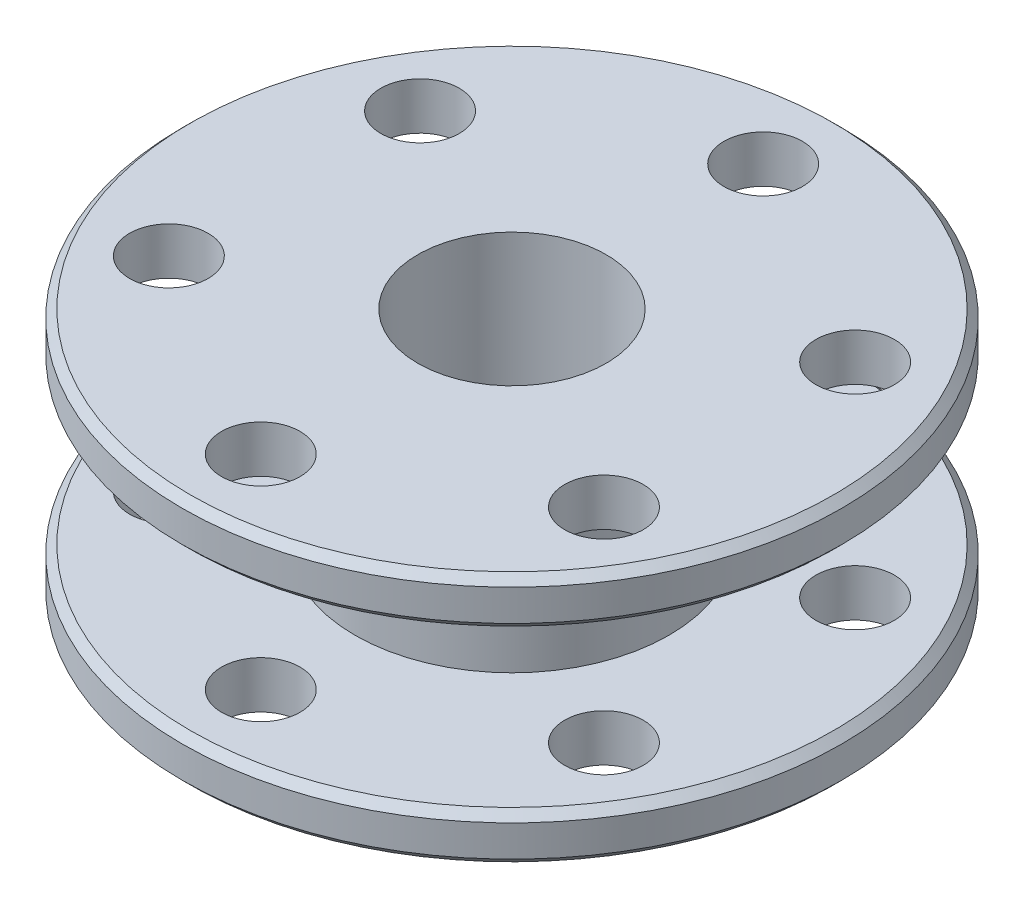
SolidWorks part; units mm, degrees
ref_plane "Front Plane" through (0, 0, 0) normal (0, 0, 1) x (1, 0, 0)
ref_plane "Top Plane" through (0, 0, 0) normal (0, 1, 0) x (1, 0, 0)
ref_plane "Right Plane" through (0, 0, 0) normal (1, 0, 0) x (0, 0, -1)
sketch "Sketch1" plane through (0, 0, 0) normal (0, 0, 1) x (1, 0, 0)
  line L0 (-6, 8) -> (-6, -8)
  line L1 (-6, -8) -> (-21, -8)
  line L2 (-21, -8) -> (-21, -5)
  line L3 (-21, -5) -> (-10, -5)
  line L4 (-10, -5) -> (-10, 5)
  line L5 (-10, 5) -> (-21, 5)
  line L6 (-21, 5) -> (-21, 8)
  line L7 (-21, 8) -> (-6, 8)
  line L8 (0, 39.6851) -> (0, -39.6851) construction
  point P3 (-6, 0)
  point P13 (0, 0)
  dimension "D1" = 6
  dimension "D2" = 16
  dimension "D3" = 21
  dimension "D4" = 10
  dimension "D5" = 3
revolve "Revolve1" add sketch "Sketch1" angle 360 about L8
chamfer "Chamfer1" distance 0.5 angle 45 4 edges at (0, -8, 21) (0, -5, 21) (0, 5, 21) (0, 8, 21)
sketch "Sketch2" plane through (0, -8, 0) normal (0, -1, 0) x (1, 0, 0)
  circle A0 centre (0, 0) radius 16 construction
  circle A1 centre (0, 16) radius 2.5
  circle A2 centre (0, 0) radius 16 construction
  circle A3 centre (13.8564, 8) radius 2.5
  circle A4 centre (0, 0) radius 16 construction
  circle A5 centre (13.8564, -8) radius 2.5
  circle A6 centre (0, 0) radius 16 construction
  circle A7 centre (0, -16) radius 2.5
  circle A8 centre (0, 0) radius 16 construction
  circle A9 centre (-13.8564, -8) radius 2.5
  circle A10 centre (0, 0) radius 16 construction
  circle A11 centre (-13.8564, 8) radius 2.5
  point P23 (0, 0)
  dimension "D1" = 32
  dimension "D2" = 5
  dimension "D3" = 6
extrude "Cut-Extrude1" cut sketch "Sketch2" against normal through all both
